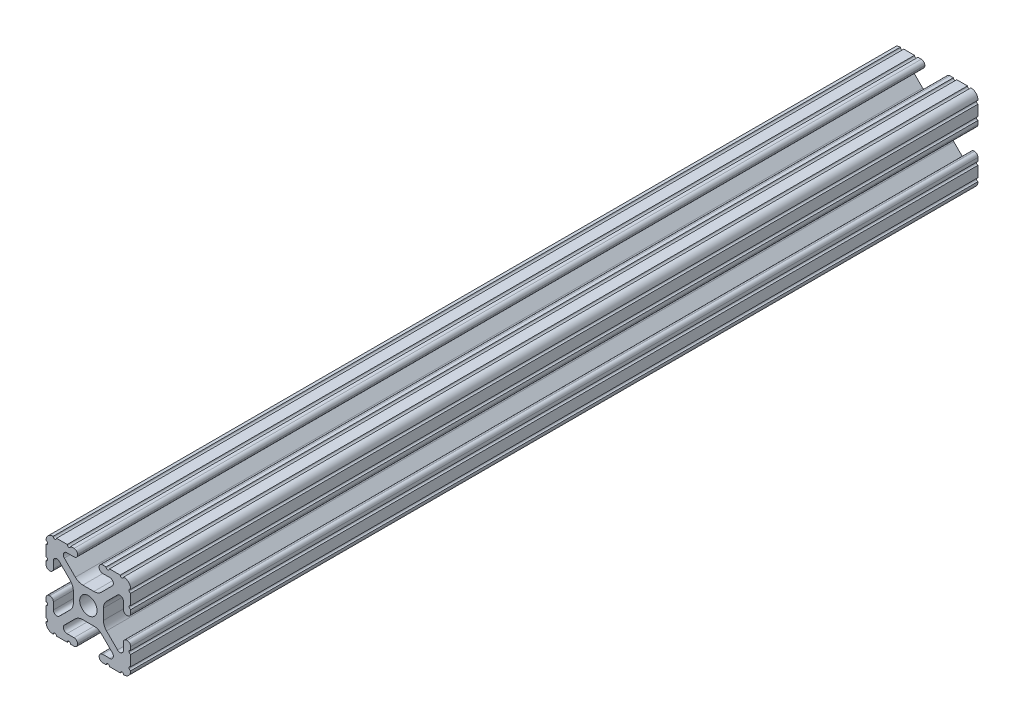
SolidWorks part; units mm, degrees
ref_plane "Front Plane" through (0, 0, 0) normal (0, 0, 1) x (1, 0, 0)
ref_plane "Top Plane" through (0, 0, 0) normal (0, 1, 0) x (1, 0, 0)
ref_plane "Right Plane" through (0, 0, 0) normal (1, 0, 0) x (0, 0, -1)
sketch "Sketch1" plane through (0, 0, 0) normal (0, 0, 1) x (1, 0, 0)
  line L0 (-7.207, 8.7244) -> (-3.8983, 5.4232)
  line L1 (-4.2875, 10.4902) -> (-6.4768, 10.4902)
  line L2 (-3.2385, 11.651) -> (-3.2385, 11.5392)
  line L3 (-5.3171, 12.7) -> (-4.2875, 12.7)
  line L4 (0, 13.4005) -> (0, -14.8534) construction
  line L5 (12.7, 0) -> (-13.9989, 0) construction
  line L6 (-9.5504, 12.7) -> (-6.3331, 12.7)
  line L7 (-12.7, 6.3331) -> (-12.7, 9.5504)
  line L8 (-12.7, 4.2875) -> (-12.7, 5.3171)
  line L9 (-11.5392, 3.2385) -> (-11.651, 3.2385)
  line L10 (-10.4902, 6.4021) -> (-10.4902, 4.2875)
  line L11 (-5.441, 3.8408) -> (-8.7371, 7.1294)
  line L12 (-4.5085, -1.5932) -> (-4.5085, 1.5932)
  line L13 (-1.7093, -4.4958) -> (1.7093, -4.4958)
  line L14 (3.9523, -5.4237) -> (7.1797, -8.6452)
  line L15 (6.4164, -10.4902) -> (4.2875, -10.4902)
  line L16 (3.2385, -11.5392) -> (3.2385, -11.651)
  line L17 (4.2875, -12.7) -> (5.3171, -12.7)
  line L18 (6.3331, -12.7) -> (9.5504, -12.7)
  line L19 (12.7, -9.5504) -> (12.7, -6.3331)
  line L20 (12.7, -5.3171) -> (12.7, -4.2875)
  line L21 (11.651, -3.2385) -> (11.5392, -3.2385)
  line L22 (10.4902, -4.2875) -> (10.4902, -6.4021)
  line L23 (8.7371, -7.1294) -> (5.441, -3.8408)
  line L24 (4.5085, -1.5932) -> (4.5085, 1.5932)
  line L25 (5.441, 3.8408) -> (8.7371, 7.1294)
  line L26 (10.4902, 6.4021) -> (10.4902, 4.2875)
  line L27 (11.5392, 3.2385) -> (11.651, 3.2385)
  line L28 (12.7, 4.2875) -> (12.7, 5.3171)
  line L29 (12.7, 6.3331) -> (12.7, 9.5504)
  line L30 (9.5504, 12.7) -> (6.3331, 12.7)
  line L31 (5.3171, 12.7) -> (4.2875, 12.7)
  line L32 (3.2385, 11.651) -> (3.2385, 11.5392)
  line L33 (4.2875, 10.4902) -> (6.4768, 10.4902)
  line L34 (7.207, 8.7244) -> (3.8983, 5.4232)
  line L35 (1.6558, 4.4958) -> (-1.6558, 4.4958)
  line L36 (-8.7371, -7.1294) -> (-5.441, -3.8408)
  line L37 (-10.4902, -4.2875) -> (-10.4902, -6.4021)
  line L38 (-11.651, -3.2385) -> (-11.5392, -3.2385)
  line L39 (-12.7, -5.3171) -> (-12.7, -4.2875)
  line L40 (-12.7, -9.5504) -> (-12.7, -6.3331)
  line L41 (-6.3331, -12.7) -> (-9.5504, -12.7)
  line L42 (-4.2875, -12.7) -> (-5.3171, -12.7)
  line L43 (-3.2385, -11.5392) -> (-3.2385, -11.651)
  line L44 (-6.4164, -10.4902) -> (-4.2875, -10.4902)
  line L45 (-3.9523, -5.4237) -> (-7.1797, -8.6452)
  arc A0 (-7.207, 8.7244) -> (-6.4768, 10.4902) centre (-6.4768, 9.4563) cw
  arc A1 (-3.2385, 11.5392) -> (-4.2875, 10.4902) centre (-4.2875, 11.5392) cw
  arc A2 (-4.2875, 12.7) -> (-3.2385, 11.651) centre (-4.2875, 11.651) cw
  arc A3 (-5.3171, 12.7) -> (-6.3331, 12.7) centre (-5.8251, 12.7) cw
  arc A4 (-9.5504, 12.7) -> (-10.5664, 12.6998) centre (-10.0584, 12.7) cw
  arc A5 (-12.6998, 10.5664) -> (-10.5664, 12.6998) centre (-10.5918, 10.5918) cw
  arc A6 (-12.6998, 10.5664) -> (-12.7, 9.5504) centre (-12.7, 10.0584) cw
  arc A7 (-12.7, 6.3331) -> (-12.7, 5.3171) centre (-12.7, 5.8251) cw
  arc A8 (-11.651, 3.2385) -> (-12.7, 4.2875) centre (-11.651, 4.2875) cw
  arc A9 (-10.4902, 4.2875) -> (-11.5392, 3.2385) centre (-11.5392, 4.2875) cw
  circle A10 centre (0, 0) radius 2.6035
  arc A11 (-10.4902, 6.4021) -> (-8.7371, 7.1294) centre (-9.4628, 6.4021) cw
  arc A12 (-5.441, 3.8408) -> (-4.5085, 1.5932) centre (-7.6835, 1.5932) cw
  arc A13 (-4.5085, -1.5932) -> (-5.441, -3.8408) centre (-7.6835, -1.5932) cw
  arc A14 (-8.7371, -7.1294) -> (-10.4902, -6.4021) centre (-9.4628, -6.4021) cw
  arc A15 (-1.7093, -4.4958) -> (-3.9523, -5.4237) centre (-1.7093, -7.6708) ccw
  arc A16 (3.9523, -5.4237) -> (1.7093, -4.4958) centre (1.7093, -7.6708) ccw
  arc A17 (6.4164, -10.4902) -> (7.1797, -8.6452) centre (6.4164, -9.4098) ccw
  arc A18 (4.2875, -10.4902) -> (3.2385, -11.5392) centre (4.2875, -11.5392) ccw
  arc A19 (3.2385, -11.651) -> (4.2875, -12.7) centre (4.2875, -11.651) ccw
  arc A20 (6.3331, -12.7) -> (5.3171, -12.7) centre (5.8251, -12.7) ccw
  arc A21 (10.5664, -12.6998) -> (9.5504, -12.7) centre (10.0584, -12.7) ccw
  arc A22 (10.5664, -12.6998) -> (12.6998, -10.5664) centre (10.5918, -10.5918) ccw
  arc A23 (12.7, -9.5504) -> (12.6998, -10.5664) centre (12.7, -10.0584) ccw
  arc A24 (12.7, -5.3171) -> (12.7, -6.3331) centre (12.7, -5.8251) ccw
  arc A25 (12.7, -4.2875) -> (11.651, -3.2385) centre (11.651, -4.2875) ccw
  arc A26 (11.5392, -3.2385) -> (10.4902, -4.2875) centre (11.5392, -4.2875) ccw
  arc A27 (8.7371, -7.1294) -> (10.4902, -6.4021) centre (9.4628, -6.4021) ccw
  arc A28 (4.5085, -1.5932) -> (5.441, -3.8408) centre (7.6835, -1.5932) ccw
  arc A29 (5.441, 3.8408) -> (4.5085, 1.5932) centre (7.6835, 1.5932) ccw
  arc A30 (10.4902, 6.4021) -> (8.7371, 7.1294) centre (9.4628, 6.4021) ccw
  arc A31 (10.4902, 4.2875) -> (11.5392, 3.2385) centre (11.5392, 4.2875) ccw
  arc A32 (11.651, 3.2385) -> (12.7, 4.2875) centre (11.651, 4.2875) ccw
  arc A33 (12.7, 6.3331) -> (12.7, 5.3171) centre (12.7, 5.8251) ccw
  arc A34 (12.6998, 10.5664) -> (12.7, 9.5504) centre (12.7, 10.0584) ccw
  arc A35 (12.6998, 10.5664) -> (10.5664, 12.6998) centre (10.5918, 10.5918) ccw
  arc A36 (9.5504, 12.7) -> (10.5664, 12.6998) centre (10.0584, 12.7) ccw
  arc A37 (5.3171, 12.7) -> (6.3331, 12.7) centre (5.8251, 12.7) ccw
  arc A38 (4.2875, 12.7) -> (3.2385, 11.651) centre (4.2875, 11.651) ccw
  arc A39 (3.2385, 11.5392) -> (4.2875, 10.4902) centre (4.2875, 11.5392) ccw
  arc A40 (7.207, 8.7244) -> (6.4768, 10.4902) centre (6.4768, 9.4563) ccw
  arc A41 (1.6558, 4.4958) -> (3.8983, 5.4232) centre (1.6558, 7.6708) ccw
  arc A42 (-1.6558, 4.4958) -> (-3.8983, 5.4232) centre (-1.6558, 7.6708) cw
  arc A43 (-11.5392, -3.2385) -> (-10.4902, -4.2875) centre (-11.5392, -4.2875) cw
  arc A44 (-12.7, -4.2875) -> (-11.651, -3.2385) centre (-11.651, -4.2875) cw
  arc A45 (-12.7, -5.3171) -> (-12.7, -6.3331) centre (-12.7, -5.8251) cw
  arc A46 (-12.7, -9.5504) -> (-12.6998, -10.5664) centre (-12.7, -10.0584) cw
  arc A47 (-10.5664, -12.6998) -> (-12.6998, -10.5664) centre (-10.5918, -10.5918) cw
  arc A48 (-10.5664, -12.6998) -> (-9.5504, -12.7) centre (-10.0584, -12.7) cw
  arc A49 (-6.3331, -12.7) -> (-5.3171, -12.7) centre (-5.8251, -12.7) cw
  arc A50 (-3.2385, -11.651) -> (-4.2875, -12.7) centre (-4.2875, -11.651) cw
  arc A51 (-4.2875, -10.4902) -> (-3.2385, -11.5392) centre (-4.2875, -11.5392) cw
  arc A52 (-6.4164, -10.4902) -> (-7.1797, -8.6452) centre (-6.4164, -9.4098) cw
  dimension "D1" = 5.207
  dimension "D9" = 14.859
  dimension "D2" = 25.4
  dimension "D3" = 12.7
  dimension "D4" = 6.477
  dimension "D5" = 8.2042
  dimension "D6" = 9.017
  dimension "D8" = 2.2098
  dimension "D10" = 2.2098
extrude "Extrude1" add sketch "Sketch1" against normal blind 254
